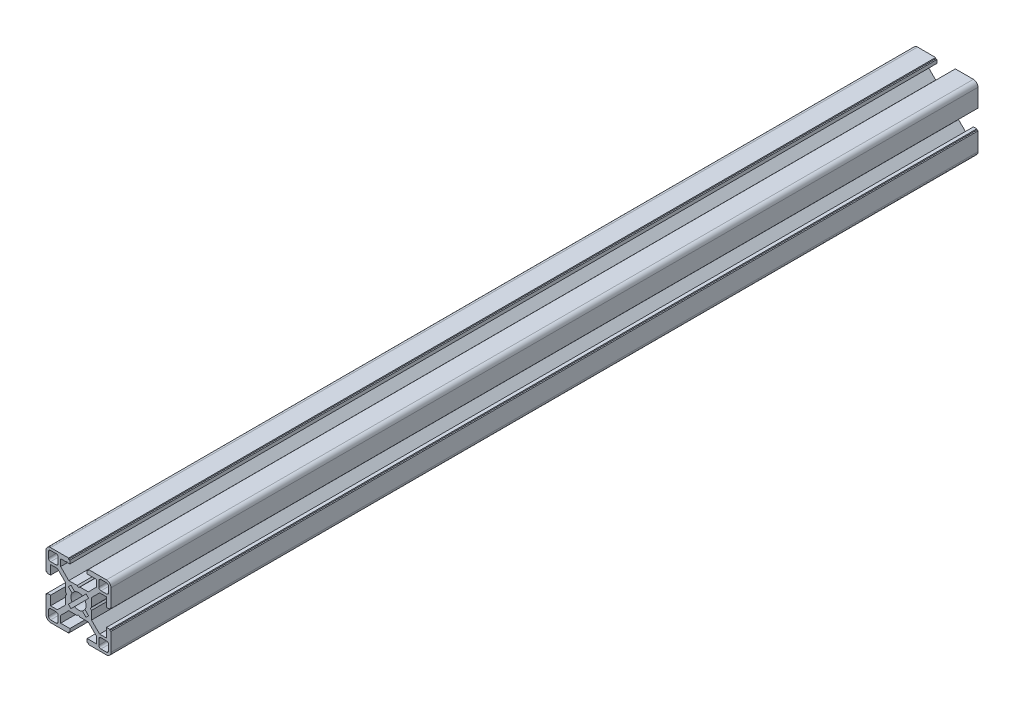
SolidWorks part; units mm, degrees
material "6061-T6 (SS)"
ref_plane "Front Plane" through (0, 0, 0) normal (0, 0, 1) x (1, 0, 0)
ref_plane "Top Plane" through (0, 0, 0) normal (0, 1, 0) x (1, 0, 0)
ref_plane "Right Plane" through (0, 0, 0) normal (1, 0, 0) x (0, 0, -1)
sketch "Sketch2" plane through (0, 0, 0) normal (0, 0, 1) x (1, 0, 0)
  line L0 (0, 15) -> (0, -15) construction
  line L1 (-15, 0) -> (15, 0) construction
  line L2 (4, -15) -> (15, -15)
  line L3 (15, -15) -> (15, -4)
  line L4 (4, -15) -> (4, -12.885)
  line L6 (8.25, -9.7455) -> (4.5045, -6)
  line L7 (0, 0) -> (15, -15) construction
  line L8 (15, -4) -> (12.885, -4)
  line L11 (4.55, -15) -> (4.55, -14.45) construction
  line L12 (4, -12.885) -> (8.25, -12.885)
  line L13 (8.25, -12.885) -> (8.25, -9.7455)
  line L14 (4.55, -14.45) -> (4, -14.45) construction
  line L15 (14.45, -4) -> (14.45, -4.55) construction
  line L16 (14.45, -4.55) -> (15, -4.55) construction
  line L17 (12.885, -4) -> (12.885, -8.25)
  line L18 (12.885, -8.25) -> (9.7455, -8.25)
  line L19 (9.7455, -8.25) -> (6, -4.5045)
  line L20 (7.8728, -6.3772) -> (6.3772, -7.8728) construction
  line L21 (11.625, -13.875) -> (11.625, -15) construction
  line L22 (9.375, -13.875) -> (13.875, -13.875)
  line L23 (9.375, -13.875) -> (9.375, -9.375)
  line L24 (9.375, -9.375) -> (13.875, -9.375)
  line L25 (13.875, -13.875) -> (13.875, -9.375)
  line L26 (11.625, -9.375) -> (11.625, -13.875) construction
  line L27 (9.375, -11.625) -> (13.875, -11.625) construction
  line L28 (13.875, -11.625) -> (15, -11.625) construction
  line L29 (8.25, -12.885) -> (9.375, -12.885) construction
  line L30 (4.5045, -6) -> (0.6555, -6)
  line L31 (0.6555, -6) -> (0, -5.45)
  line L32 (0, -6) -> (0, -5.45) construction
  circle A0 centre (0, 0) radius 3.5
  arc A2 (9.375, -12.885) -> (10.365, -13.875) centre (10.365, -12.885) ccw construction
  point P8 (0, -6)
  point P15 (4.55, -15)
  point P16 (7.125, -7.125)
  point P33 (11.625, -11.625)
  dimension "Center Hole Diameter" = 7
  dimension "Rail Height" = 30
  dimension "Rail Width" = 30
  dimension "T-Slot Width" = 8
  dimension "Slot Depth" = 9
  dimension "Slot Inner Width" = 16.5
  dimension "Step Width" = 9.1
  dimension "D1" = 1.125
  dimension "D2" = 2.115
  dimension "D3" = 50
sketch "Sketch3" plane through (0, 0, 0) normal (1, 0, 0) x (0, 0, -1)
  line L0 (-76.2, -15) -> (76.2, -15) construction
  line L1 (-50.8, 0) -> (50.8, 0) construction
  point P6 (-50.8, 0)
  point P8 (50.8, 0)
  dimension "Length" = 152.4
  dimension "D1" = 25.4
sketch "Sketch4" plane through (0, 0, 0) normal (0, 0, 1) x (1, 0, 0)
  line L22 (0, -5.45) -> (0.6555, -6)
  line L23 (0.6555, -6) -> (4.5045, -6)
  line L24 (4.5045, -6) -> (8.25, -9.7455)
  line L25 (8.25, -9.7455) -> (8.25, -12.885)
  line L26 (8.25, -12.885) -> (4, -12.885)
  line L27 (4, -12.885) -> (4, -14.45)
  line L28 (4, -14.45) -> (4.55, -14.45)
  line L29 (4.55, -14.45) -> (4.55, -15)
  line L30 (4.55, -15) -> (12.885, -15)
  line L31 (4, -15) -> (15, -15) construction
  line L32 (15, -15) -> (15, -4) construction
  line L33 (15, -12.885) -> (15, -4.55)
  line L34 (15, -4.55) -> (14.45, -4.55)
  line L35 (14.45, -4.55) -> (14.45, -4)
  line L36 (14.45, -4) -> (12.885, -4)
  line L37 (12.885, -4) -> (12.885, -8.25)
  line L38 (12.885, -8.25) -> (9.7455, -8.25)
  line L39 (9.7455, -8.25) -> (6, -4.5045)
  line L40 (6, -4.5045) -> (6, -0.6555)
  line L41 (6, -0.6555) -> (5.45, 0)
  line L42 (-15, 0) -> (15, 0) construction
  line L43 (0, -5.45) -> (0, -3.5)
  line L44 (0, 15) -> (0, -15) construction
  line L45 (3.5, 0) -> (5.45, 0)
  line L46 (1.8108, -2.9952) -> (3.4913, -4.6757)
  line L47 (3.4913, -4.6757) -> (4.6757, -3.4913)
  line L48 (4.6757, -3.4913) -> (2.9952, -1.8108)
  line L49 (0, 0) -> (15, -15) construction
  line L50 (9.375, -13.875) -> (13.875, -13.875) construction
  line L51 (13.875, -13.875) -> (13.875, -9.375) construction
  line L52 (9.375, -13.875) -> (9.375, -9.375) construction
  line L53 (9.375, -9.375) -> (13.875, -9.375) construction
  line L54 (9.375, -10.365) -> (9.375, -12.885)
  line L55 (10.365, -13.875) -> (12.885, -13.875)
  line L56 (13.875, -12.885) -> (13.875, -10.365)
  line L57 (10.365, -9.375) -> (12.885, -9.375)
  arc A12 (12.885, -15) -> (15, -12.885) centre (12.885, -12.885) ccw
  circle A13 centre (0, 0) radius 3.5 construction
  arc A14 (0, -3.5) -> (1.8108, -2.9952) centre (0, 0) ccw
  arc A15 (3.5, 0) -> (2.9952, -1.8108) centre (0, 0) cw
  circle A16 centre (0, 0) radius 5.775 construction
  arc A17 (9.375, -12.885) -> (10.365, -13.875) centre (10.365, -12.885) ccw
  arc A18 (9.375, -12.885) -> (10.365, -13.875) centre (10.365, -12.885) ccw construction
  arc A19 (12.885, -13.875) -> (13.875, -12.885) centre (12.885, -12.885) ccw
  arc A20 (9.375, -10.365) -> (10.365, -9.375) centre (10.365, -10.365) cw
  arc A21 (12.885, -9.375) -> (13.875, -10.365) centre (12.885, -10.365) cw
  point P40 (4.0835, -4.0835)
  dimension "D1" = 11.55
  dimension "D2" = 0.22
extrude "Boss-Extrude1" add sketch "Sketch4" along normal mid plane 400
mirror "Mirror1" about plane through (0, 0, 0) normal (1, 0, 0) of bodies 134
mirror "Mirror2" about plane through (0, 0, 0) normal (0, 1, 0) of bodies 135
sketch "Sketch5" plane through (0, 0, 200) normal (0, 0, 1) x (1, 0, 0)
  line L0 (-5.675, 12.885) -> (-5.4, 13.16)
  line L1 (-8.25, 12.885) -> (-4, 12.885) construction
  line L2 (-5.4, 13.16) -> (-5.125, 12.885)
  line L3 (0, 15) -> (0, -15) construction
  line L4 (-5.675, 12.885) -> (-5.125, 12.885)
  dimension "D1" = 0.275
  dimension "D2" = 5.4
extrude "Cut-Extrude1" cut sketch "Sketch5" against normal through all both and the other way through all
sketch "Sketch6" plane through (0, 0, 200) normal (0, 0, 1) x (1, 0, 0)
  line L0 (-15, 4.55) -> (-15, -4.55) construction
  line L1 (15, 4.55) -> (15, -4.55) construction
  line L2 (-4.55, 15) -> (4.55, 15) construction
  line L3 (4.55, -15) -> (-4.55, -15) construction
  point P16 (0, 15)
  point P17 (15, 0)
  point P18 (0, -15)
  point P19 (-15, 0)
equation "\"D1@Boss-Extrude1\"=\"Length@Sketch3\""
equation "\"D1@Sketch2\"=\"Slot Depth@Sketch2\"*0.125"
equation "\"D2@Sketch2\"=\"Slot Depth@Sketch2\"*0.235"
equation "\"D1@Sketch4\"=\"Center Hole Diameter@Sketch2\"*1.65"
equation "\"D2@Sketch4\"=(\"Step Width@Sketch2\"-\"T-Slot Width@Sketch2\")*0.2"
equation "\"D1@Sketch5\"=(\"Step Width@Sketch2\"-\"T-Slot Width@Sketch2\")*0.5*0.5"
equation "\"D2@Sketch5\"=\"T-Slot Width@Sketch2\"*1.35*0.5"
